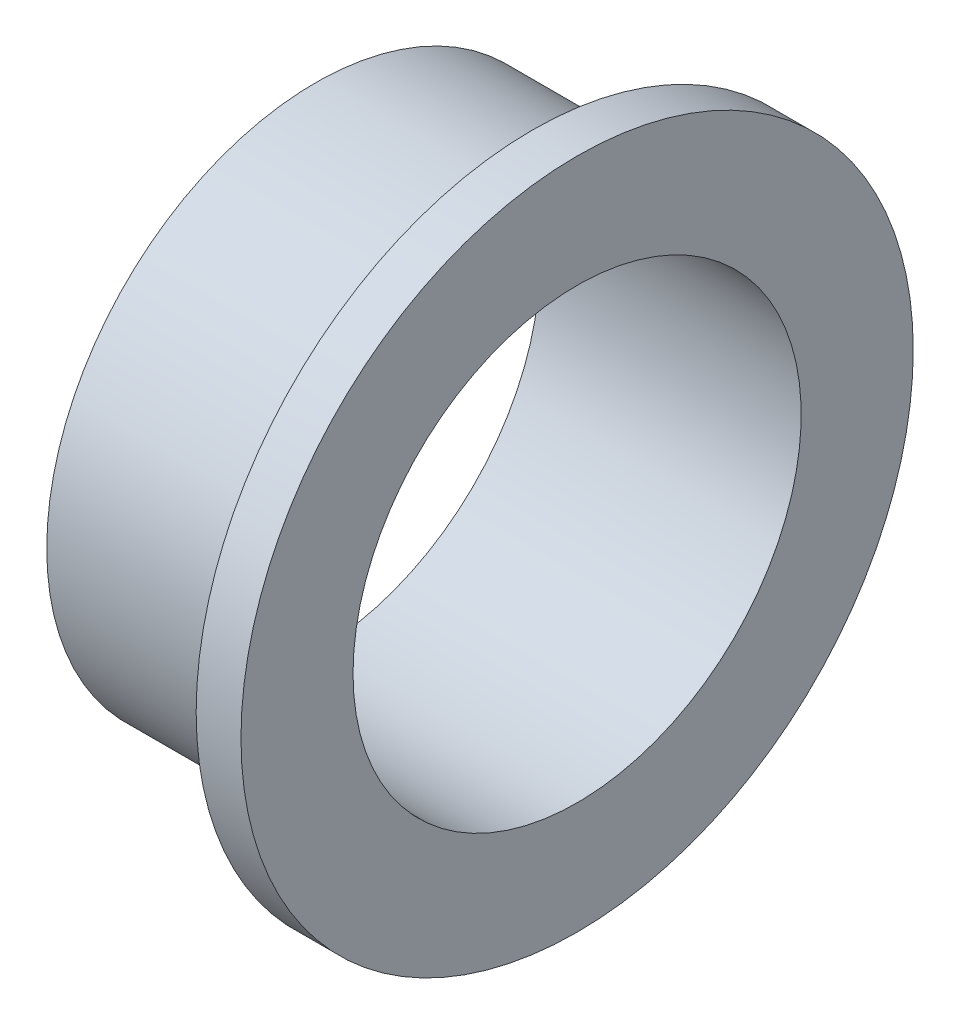
SolidWorks part; units mm, degrees
material "Brass"
ref_plane "Front Plane" through (0, 0, 0) normal (0, 0, 1) x (1, 0, 0)
ref_plane "Top Plane" through (0, 0, 0) normal (0, 1, 0) x (1, 0, 0)
ref_plane "Right Plane" through (0, 0, 0) normal (1, 0, 0) x (0, 0, -1)
sketch "Sketch1" plane through (0, 0, 0) normal (0, 0, 1) x (1, 0, 0)
  line L0 (-57.1233, 0) -> (0, 0) construction
  line L1 (0, 0) -> (0, 56.0959) construction
  line L2 (-35, 30) -> (0, 30)
  line L3 (0, 30) -> (0, 45)
  line L4 (-35, 36) -> (-6, 36)
  line L5 (-6, 36) -> (-6, 45)
  line L6 (-6, 45) -> (0, 45)
  line L7 (-35, 36) -> (-35, 30)
  dimension "D1" = 60
  dimension "D2" = 90
  dimension "D3" = 35
  dimension "D4" = 6
revolve "Revolve1" add sketch "Sketch1" angle 360 about L0
